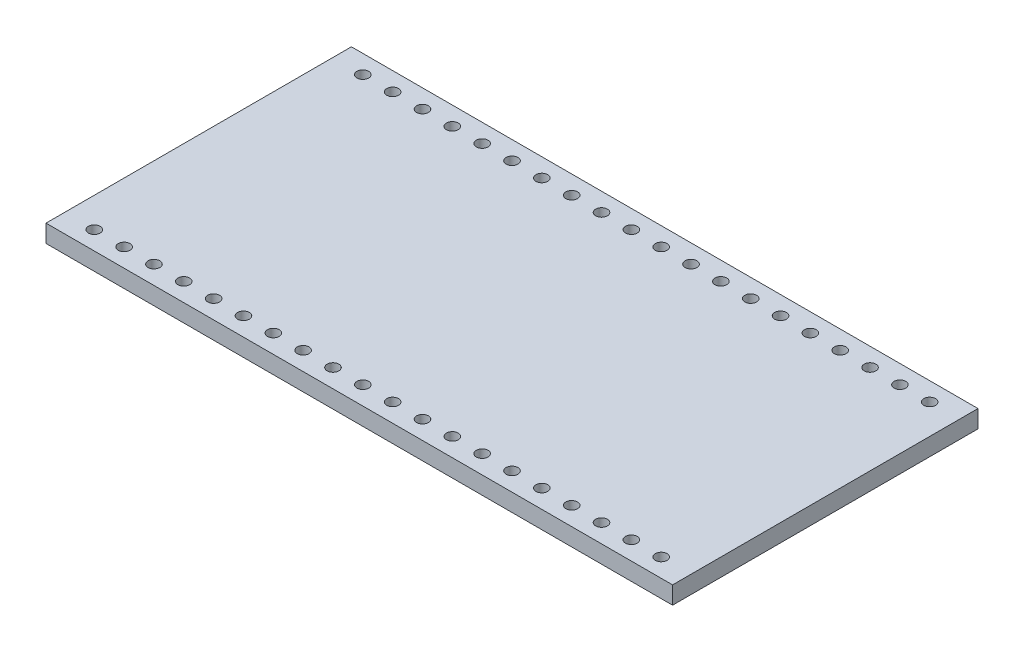
SolidWorks part; units mm, degrees
ref_plane "Front Plane" through (0, 0, 0) normal (0, 0, 1) x (1, 0, 0)
ref_plane "Top Plane" through (0, 0, 0) normal (0, 1, 0) x (1, 0, 0)
ref_plane "Right Plane" through (0, 0, 0) normal (1, 0, 0) x (0, 0, -1)
sketch "Sketch1" plane through (0, 0, 0) normal (0, 1, 0) x (1, 0, 0)
  line L1 (0, 0) -> (53.34, 0)
  line L2 (0, 0) -> (0, 26)
  line L3 (0, 26) -> (53.34, 26)
  line L4 (53.34, 0) -> (53.34, 26)
  dimension "D1" = 26
  dimension "D2" = 53.34
extrude "Boss-Extrude1" add sketch "Sketch1" along normal blind 1.5
sketch "Sketch2" plane through (0, 1.5, 0) normal (0, 1, 0) x (1, 0, 0)
  line L0 (0, 26) -> (0, 0) construction
  line L1 (0, 0) -> (53.34, 0) construction
  circle A0 centre (2.54, 1.57) radius 0.5
  circle A1 centre (2.54, 24.43) radius 0.5
  dimension "D4" = 1
  dimension "D1" = 22.86
  dimension "D2" = 2.54
  dimension "D3" = 1.57
extrude "Cut-Extrude1" cut sketch "Sketch2" against normal up to next (1.5 mm away)
pattern_linear "LPattern1" count 20 spacing 2.54 along (1, 0, 0) of "Cut-Extrude1"
